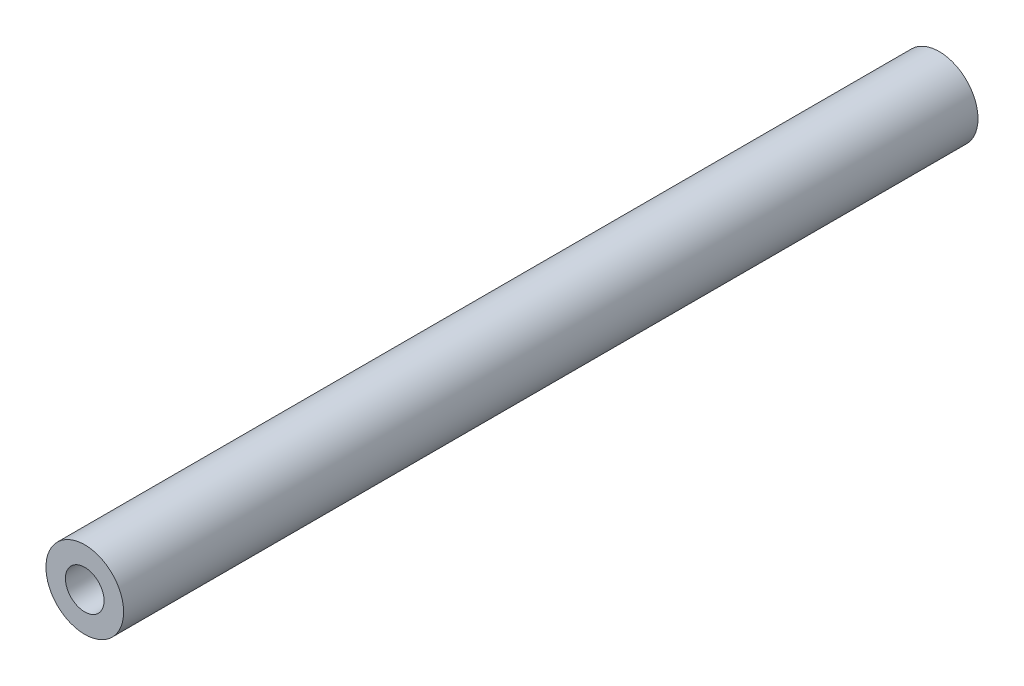
SolidWorks part; units mm, degrees
ref_plane "Front Plane" through (0, 0, 0) normal (0, 0, 1) x (1, 0, 0)
ref_plane "Top Plane" through (0, 0, 0) normal (0, 1, 0) x (1, 0, 0)
ref_plane "Right Plane" through (0, 0, 0) normal (1, 0, 0) x (0, 0, -1)
sketch "Sketch2" plane through (0, 0, 0) normal (0, 0, 1) x (1, 0, 0)
  circle A0 centre (0, 0) radius 25.3947
  circle A1 centre (0, 0) radius 12.6385
extrude "Boss-Extrude1" add sketch "Sketch2" along normal blind 558.8
